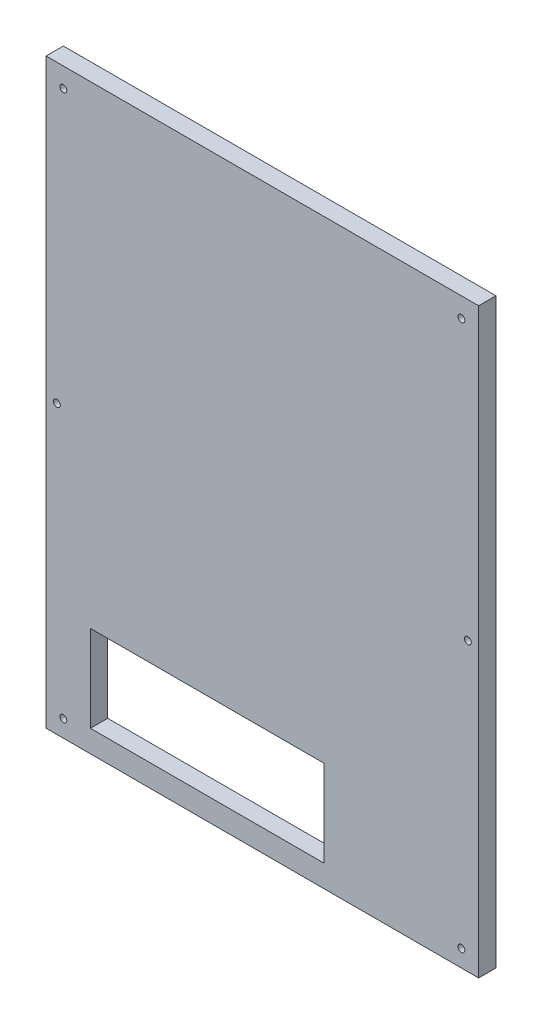
SolidWorks part; units mm, degrees
ref_plane "Alzado" through (0, 0, 0) normal (0, 0, 1) x (1, 0, 0)
ref_plane "Planta" through (0, 0, 0) normal (0, 1, 0) x (1, 0, 0)
ref_plane "Vista lateral" through (0, 0, 0) normal (1, 0, 0) x (0, 0, -1)
sketch "Croquis1" plane through (0, 0, 0) normal (0, 0, 1) x (1, 0, 0)
  line L1 (-125, 168.21) -> (125, 168.21)
  line L2 (-125, 168.21) -> (-125, -168.21)
  line L3 (-125, -168.21) -> (125, -168.21)
  line L4 (125, 168.21) -> (125, -168.21)
  line L5 (-125, 168.21) -> (125, -168.21) construction
  line L6 (-125, -168.21) -> (125, 168.21) construction
  point P0 (0, 0)
  dimension "D1" = 250
  dimension "D2" = 336.42
extrude "Saliente-Extruir1" add sketch "Croquis1" along normal blind 10
sketch "Croquis2" plane through (0, 0, 0) normal (0, 0, -1) x (-1, 0, 0)
  line L0 (-115, 156.8818) -> (-118.75, -2.4727) construction
  line L1 (-118.75, -2.4727) -> (-115, -158.3881) construction
  line L2 (-115, -158.3881) -> (115, -158.3881) construction
  line L3 (115, -158.3881) -> (118.75, -2.4727) construction
  line L4 (118.75, -2.4727) -> (115, 156.8818) construction
  line L5 (115, 156.8818) -> (-115, 156.8818) construction
  line L6 (-115, 156.8818) -> (-125, 168.21) construction
  circle A0 centre (115, 156.8818) radius 2
  circle A1 centre (-115, 156.8818) radius 2
  circle A2 centre (-118.75, -2.4727) radius 2
  circle A3 centre (118.75, -2.4727) radius 2
  circle A4 centre (-115, -158.3881) radius 2
  circle A5 centre (115, -158.3881) radius 2
extrude "Cortar-Extruir1" cut sketch "Croquis2" against normal up to next
sketch "Croquis3" plane through (0, 0, 0) normal (0, 0, -1) x (-1, 0, 0)
  line L1 (-35.6393, -105.422) -> (99.3607, -105.422)
  line L2 (-35.6393, -105.422) -> (-35.6393, -155.422)
  line L3 (-35.6393, -155.422) -> (99.3607, -155.422)
  line L4 (99.3607, -105.422) -> (99.3607, -155.422)
  point P4 (0, 0)
  dimension "D1" = 135
  dimension "D2" = 50
extrude "Cortar-Extruir2" cut sketch "Croquis3" against normal up to next
